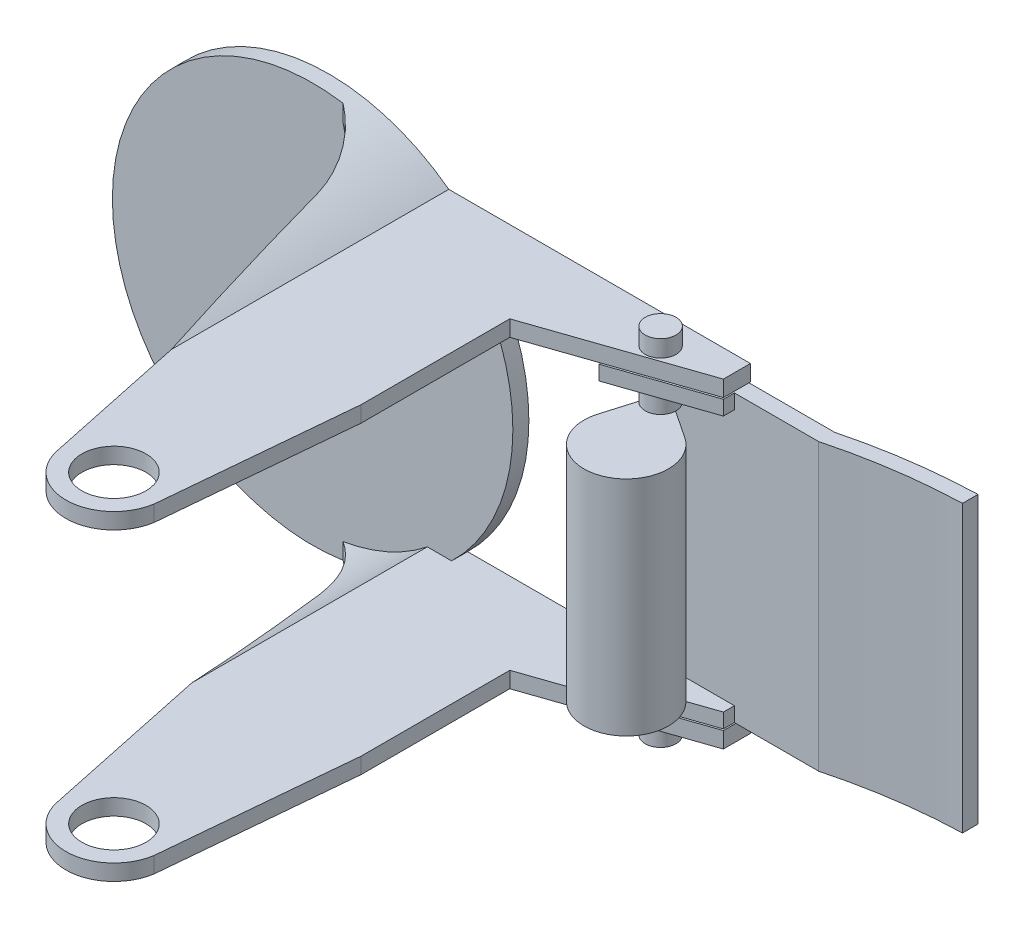
SolidWorks part; units mm, degrees
ref_plane "前视基准面" through (0, 0, 0) normal (0, 0, 1) x (1, 0, 0)
ref_plane "上视基准面" through (0, 0, 0) normal (0, 1, 0) x (1, 0, 0)
ref_plane "右视基准面" through (0, 0, 0) normal (1, 0, 0) x (0, 0, -1)
sketch "草图1" plane through (0, 0, 0) normal (0, 0, 1) x (1, 0, 0)
  line L0 (59.8768, 20) -> (63.0859, 20)
  line L1 (15, -20) -> (32.808, -20)
  line L2 (59.8768, -20) -> (59.8768, 20)
  line L3 (32.808, 20) -> (15, 20)
  line L4 (63.0859, 20) -> (63.0859, 18)
  line L5 (0, 50.776) -> (0, -82.3073)
  line L6 (63.0859, 18) -> (59.8768, 18)
  line L7 (32.808, 20) -> (32.808, 18)
  line L8 (59.8768, -20) -> (63.0859, -20)
  line L9 (63.0859, -20) -> (63.0859, -18)
  line L10 (63.0859, -18) -> (59.8768, -18)
  line L11 (32.808, 18) -> (14.3178, 18)
  line L12 (32.808, -18) -> (32.808, -20)
  line L13 (32.808, -18) -> (14.3178, -18)
  line L14 (0, 25) -> (0, 23)
  line L15 (0, -23) -> (0, -25)
  arc A1 (15, 20) -> (0, 25) centre (0, 0) ccw
  arc A2 (14.3178, 18) -> (0, 23) centre (0, 0) ccw
  arc A3 (0, -23) -> (14.3178, -18) centre (0, 0) ccw
  arc A4 (0, -25) -> (15, -20) centre (0, 0) ccw
extrude "凸台-拉伸2" add sketch "草图1" along normal blind 57.5 contours L3 A1 L14 A2 L11 L7
sketch "草图3" plane through (0, 20, 0) normal (0, 1, 0) x (1, 0, 0)
  line L0 (32.808, 0) -> (40.7234, 0)
  line L1 (40.7234, 0) -> (40.7234, -51.5)
  circle A0 centre (24.6955, -51.5) radius 4
extrude "切除-拉伸1" cut sketch "草图3" against normal blind 57.5 contours A0
sketch "草图4" plane through (0, 20, 0) normal (0, 1, 0) x (1, 0, 0)
  line L0 (32.808, -57.5) -> (15, -57.5) construction
  line L2 (30.6256, -52.4132) -> (32.808, -28.75)
  line L3 (32.808, -57.5) -> (32.808, 0) construction
  line L4 (9.6937, -10.2252) -> (18.9407, -53.1977)
  line L5 (32.808, -28.75) -> (32.808, -57.5)
  line L6 (32.808, -57.5) -> (24.6955, -57.5)
  line L7 (24.6955, -57.5) -> (0, -57.5)
  line L8 (0, -57.5) -> (0, 0)
  arc A1 (0, 0) -> (9.6937, -10.2252) centre (-2.581, -12.1543) cw
  arc A2 (24.6955, -57.5) -> (30.6256, -52.4132) centre (24.6955, -51.5) ccw
  arc A3 (18.9407, -53.1977) -> (24.6955, -57.5) centre (24.6955, -51.5) ccw
extrude "切除-拉伸3" cut sketch "草图4" against normal blind 57.5 contours A2 L2 L5 L6
sketch "草图7" plane through (0, 18, 0) normal (0, -1, 0) x (1, 0, 0)
  line L1 (18.825, 52.74) -> (10.0436, 11.1674)
  line L2 (0, 0) -> (0, 57.5)
  line L3 (0, 57.5) -> (24.6955, 57.5)
  arc A0 (24.6955, 57.5) -> (18.825, 52.74) centre (24.6955, 51.5) ccw
  arc A2 (0, 0) -> (10.0436, 11.1674) centre (-5.5103, 15.0559) ccw
  arc A3 (30.6256, 52.4132) -> (24.6955, 57.5) centre (24.6955, 51.5) ccw construction
extrude "切除-拉伸4" cut sketch "草图7" against normal blind 57.5
sketch "草图9" plane through (0, 0, 0) normal (0, 0, -1) x (-1, 0, 0)
  line L0 (0, 0) -> (-41.2693, 0)
  circle A0 centre (0, 0) radius 25
extrude "切除-拉伸5" cut sketch "草图9" against normal blind 2 contours A0
sketch "草图14" plane through (0, 0, 0) normal (0, 0, -1) x (-1, 0, 0)
  line L3 (-32.808, -18) -> (-32.808, -20)
  line L4 (-14.3178, -18) -> (-32.808, -18)
  line L5 (-15, -20) -> (-32.808, -20)
  line L7 (-3.7949, -22.6848) -> (-3.7949, -24.7103)
  arc A0 (-15, -20) -> (-3.7949, -24.7103) centre (0, 0) ccw
  arc A1 (-14.3178, -18) -> (-3.7949, -22.6848) centre (0, 0) ccw
extrude "凸台-拉伸6" add sketch "草图14" against normal blind 57.5 separate body
sketch "草图15" plane through (0, -18, 0) normal (0, 1, 0) x (1, 0, 0)
  circle A0 centre (24.6955, -51.5) radius 4
extrude "切除-拉伸6" cut sketch "草图15" against normal blind 57.5
sketch "草图16" plane through (0, -18, 0) normal (0, 1, 0) x (1, 0, 0)
  line L0 (32.808, -28.75) -> (32.808, -57.5)
  line L2 (32.808, -28.75) -> (30.6256, -52.4132)
  line L3 (32.808, -57.5) -> (24.8616, -57.5)
  line L4 (14.3178, -57.5) -> (32.808, -57.5) construction
  line L5 (24.8616, -57.4977) -> (24.8616, -57.5)
  arc A0 (18.825, -52.74) -> (30.6256, -52.4132) centre (24.6955, -51.5) ccw construction
  arc A2 (30.6256, -52.4132) -> (24.8616, -57.4977) centre (24.6955, -51.5) cw
extrude "切除-拉伸8" cut sketch "草图16" against normal blind 57.5
sketch "草图19" plane through (0, -18, 0) normal (0, 1, 0) x (1, 0, 0)
  line L0 (24.8616, -57.4977) -> (24.8616, -57.5) construction
  line L1 (24.8616, -57.4977) -> (24.8669, -57.5026)
  line L2 (24.8669, -57.5026) -> (24.8576, -57.5032)
  line L3 (24.8576, -57.5032) -> (24.4806, -57.5426)
  line L4 (24.4806, -57.5426) -> (6.9626, -59.3759)
  line L5 (6.9626, -59.3759) -> (-10.5921, -60.4492)
  line L6 (-10.5921, -60.4492) -> (-4.9283, -45.2285)
  line L7 (-4.9283, -45.2285) -> (3.7949, -2)
  line L8 (3.7949, -2) -> (10.0436, -11.1674)
  line L9 (10.0436, -11.1674) -> (18.8356, -52.7888)
  arc A0 (18.8356, -52.7888) -> (24.8616, -57.4977) centre (24.6955, -51.5) ccw
  arc A2 (18.825, -52.74) -> (30.6256, -52.4132) centre (24.6955, -51.5) ccw construction
  arc A3 (10.0436, -11.1674) -> (3.7949, -2) centre (-5.5103, -15.0559) ccw construction
extrude "切除-拉伸9" cut sketch "草图19" against normal blind 57.5
sketch "草图20" plane through (0, -18, 0) normal (0, 1, 0) x (1, 0, 0)
  line L1 (3.7949, -2) -> (3.7949, 0) construction
  line L2 (10.0436, -11.1674) -> (3.7949, -2)
  arc A0 (10.0436, -11.1674) -> (3.7949, -2) centre (-5.5103, -15.0559) ccw
extrude "切除-拉伸10" cut sketch "草图20" against normal blind 57.5
sketch "草图21" plane through (0, -18, 0) normal (0, 1, 0) x (1, 0, 0)
  line L0 (15.2952, 2.2417) -> (15, 0)
  line L1 (15, 0) -> (15, -2) construction
  line L2 (32.808, 0) -> (15, 0) construction
  line L3 (15, 0) -> (15, -2)
  line L4 (15, -2) -> (2.3979, -2)
  line L5 (2.3979, -2) -> (2.909, 1.8811)
  line L6 (2.909, 1.8811) -> (15.2952, 2.2417)
extrude "切除-拉伸11" cut sketch "草图21" against normal blind 57.5
sketch "草图23" plane through (0, 0, 0) normal (0, 0, -1) x (-1, 0, 0)
  circle A0 centre (0, 0) radius 25
extrude "凸台-拉伸7" add sketch "草图23" against normal blind 2
sketch "草图24" plane through (0, 0, 0) normal (0, 0, -1) x (-1, 0, 0)
  circle A0 centre (0, 0) radius 3.72
extrude "切除-拉伸12" cut sketch "草图24" against normal blind 2
cosmetic thread "装饰螺纹线1" parameters "D2"=10
chamfer "倒角1" distance 0.1 angle 45 2 edges at (-3.72, 0, 2) (-3.72, 0, 0)
sketch "草图26" plane through (0, -20, 0) normal (0, -1, 0) x (1, 0, 0)
  line L0 (32.808, 0) -> (52.658, 0)
  line L2 (32.808, 28.75) -> (32.808, 0) construction
  line L3 (32.808, 10.1933) -> (32.808, 0)
  line L5 (52.658, 3.3753) -> (32.808, 10.1933)
  line L8 (52.658, 0) -> (63.1835, 0)
  line L10 (78.8361, -0.297) -> (78.8361, -2.2325)
  line L11 (63.1835, 2) -> (52.658, 2)
  line L12 (52.658, 2) -> (52.658, 3.3753)
  arc A9 (63.1835, 2) -> (78.8361, -0.297) centre (81.0041, 68.9571) ccw
  arc A10 (63.1835, 0) -> (78.8361, -2.2325) centre (81.0041, 68.9571) ccw
  circle A13 centre (53.8472, 10.9778) radius 6.5409
  circle A14 centre (51.1732, 1.3095) radius 0.9616
extrude "凸台-拉伸9" add sketch "草图26" against normal blind 40 contours L10 A10 L8 L0 L3 L5 L12 L11 A13
sketch "草图28" plane through (0, -18, 0) normal (0, 1, 0) x (1, 0, 0)
  line L4 (52.658, -2) -> (52.658, 6.3503)
  line L5 (52.658, 6.3503) -> (82.0742, 6.3503)
  line L6 (82.0742, 6.3503) -> (82.0742, -4.8171)
  line L7 (82.0742, -4.8171) -> (68.0686, -9.6913)
  line L8 (68.0686, -9.6913) -> (52.658, -2)
extrude "切除-拉伸14" cut sketch "草图28" against normal blind 15
sketch "草图29" plane through (0, 18, 0) normal (0, -1, 0) x (1, 0, 0)
  line L0 (52.658, 0) -> (52.658, 7.9653)
  line L1 (52.658, 7.9653) -> (80.9235, 6.2321)
  line L2 (80.9235, 6.2321) -> (83.7158, -14.3728)
  line L3 (83.7158, -14.3728) -> (61.474, -14.3728)
  line L4 (61.474, -14.3728) -> (52.658, 0)
extrude "切除-拉伸15" cut sketch "草图29" against normal blind 15
sketch "草图30" plane through (52.658, 0, 0) normal (1, 0, 0) x (0, 0, -1)
  line L0 (-14, 16) -> (-2, 16)
  line L2 (-2, 16) -> (-2, -16)
  line L3 (-2, -16) -> (-14, -16)
  line L4 (-14, 16) -> (-14, -16)
extrude "切除-拉伸17" cut sketch "草图30" against normal blind 27
sketch "草图31" plane through (0, 0, 0) normal (0, 0, -1) x (-1, 0, 0)
  line L0 (-32.808, 18) -> (-41.1024, 18)
  line L1 (-41.1024, 18) -> (-41.1024, -18)
  line L2 (-41.1024, -18) -> (-32.808, -18)
  line L3 (-32.808, -18) -> (-32.808, 18)
extrude "切除-拉伸18" cut sketch "草图31" against normal blind 12
sketch "草图32" plane through (0, 0, 0) normal (0, 0, -1) x (-1, 0, 0)
  line L0 (-41.1024, 18) -> (-41.1024, 17.8178)
  line L1 (-41.1024, 18) -> (-41.1024, -18) construction
  line L2 (-41.1024, 17.8178) -> (-80.4808, 17.8178)
  line L3 (-80.2984, 18.1229) -> (-78.8361, 18)
  line L4 (-78.8361, 18) -> (-78.8361, -18) construction
  line L5 (-63.1835, 18) -> (-78.8361, 18) construction
  line L6 (-78.8361, 18) -> (-41.1024, 18)
  arc A0 (-80.4808, 17.8178) -> (-80.2984, 18.1229) centre (-80.1343, 17.8178) cw
extrude "切除-拉伸19" cut sketch "草图32" against normal blind 12
sketch "草图33" plane through (0, 0, 0) normal (0, 0, -1) x (-1, 0, 0)
  line L0 (-41.1024, 17.8178) -> (-41.1024, 18)
  line L1 (-52.658, 18) -> (-17.3494, 18) construction
  line L2 (-41.1024, 18) -> (-90.8654, 18)
  line L3 (-90.8654, 18) -> (-92.5652, 18)
  line L4 (-92.5652, 18) -> (-78.8361, 17.8178)
  line L5 (-78.8361, 18) -> (-78.8361, -18) construction
  line L6 (-78.8361, 17.8178) -> (-41.1024, 17.8178)
extrude "切除-拉伸20" cut sketch "草图33" along normal blind 12
sketch "草图34" plane through (0, 0, 0) normal (0, 0, -1) x (-1, 0, 0)
  line L0 (-41.1024, -18) -> (-41.1024, -17.8245)
  line L1 (-41.1024, 17.8178) -> (-41.1024, -18) construction
  line L2 (-41.1024, -17.8245) -> (-87.5995, -17.8245)
  line L3 (-87.5995, -17.8245) -> (-86.5877, -19.8267)
  line L4 (-86.5877, -19.8267) -> (-63.1835, -18)
  line L5 (-63.1835, -18) -> (-41.1024, -18)
extrude "切除-拉伸23" cut sketch "草图34" against normal blind 12
sketch "草图35" plane through (0, 0, 0) normal (0, 0, -1) x (-1, 0, 0)
  line L0 (-63.1835, -17.8245) -> (-63.0127, -20.6234)
  line L1 (-63.0127, -20.6234) -> (-79.2371, -22.4118)
  line L2 (-79.2371, -22.4118) -> (-80.6807, -17.0467)
  line L3 (-80.6807, -17.0467) -> (-78.8361, -17.8245)
  line L4 (-78.8361, 17.8178) -> (-78.8361, -18) construction
  line L5 (-78.8361, -17.8245) -> (-63.1835, -17.8245)
extrude "切除-拉伸24" cut sketch "草图35" along normal blind 20
sketch "草图36" plane through (0, 16, 0) normal (0, -1, 0) x (1, 0, 0)
  circle A0 centre (45.1163, 3.6691) radius 1.4674
extrude "切除-拉伸25" cut sketch "草图36" against normal blind 20
sketch "草图37" plane through (0, 16, 0) normal (0, -1, 0) x (1, 0, 0)
  circle A0 centre (45.1163, 3.6691) radius 1.4674
extrude "切除-拉伸26" cut sketch "草图37" along normal blind 41
sketch "草图38" plane through (0, -20, 0) normal (0, -1, 0) x (1, 0, 0)
  circle A2 centre (45.1163, 3.6691) radius 1.92
extrude "凸台-拉伸11" add sketch "草图38" along normal blind 2.1
move or copy body "实体-移动/复制1" bodies to move or copy 145 placed by mates yes parameters "D1"=0, "D2"=0, "D3"=0
sketch "草图40" plane through (0, -16, 0) normal (0, 1, 0) x (1, 0, 0)
  circle A0 centre (45.1163, -3.6691) radius 1.92
extrude "凸台-拉伸12" add sketch "草图40" along normal blind 2.1
sketch "草图41" plane through (0, 20, 0) normal (0, 1, 0) x (1, 0, 0)
  circle A0 centre (45.1163, -3.6691) radius 1.92
extrude "凸台-拉伸13" add sketch "草图41" along normal blind 2.1
sketch "草图42" plane through (0, 16, 0) normal (0, -1, 0) x (1, 0, 0)
  circle A0 centre (45.1163, 3.6691) radius 1.92
extrude "凸台-拉伸14" add sketch "草图42" along normal blind 2.1
sketch "草图44" plane through (0, 13.9, 0) normal (0, -1, 0) x (1, 0, 0)
  circle A0 centre (45.1163, 3.6691) radius 1.019
extrude "凸台-拉伸15" add sketch "草图44" along normal blind 28.1
sketch "草图45" plane through (0, -13.9, 0) normal (0, 1, 0) x (1, 0, 0)
  line L0 (45.6812, -2.8211) -> (50.4848, -6.0207)
  line L1 (44.1393, -3.3798) -> (42.5007, -8.914)
  line L2 (45.6812, -2.8211) -> (44.1393, -3.3798)
  arc A0 (42.5007, -8.914) -> (50.4848, -6.0207) centre (47.5598, -10.412) ccw
  circle A1 centre (45.1163, -3.6691) radius 1.019 construction
extrude "凸台-拉伸16" add sketch "草图45" along normal blind 2.1
sketch "草图46" plane through (0, 13.9, 0) normal (0, -1, 0) x (1, 0, 0)
  line L0 (50.4848, 6.0207) -> (45.6812, 2.8211)
  line L1 (50.4848, 6.0207) -> (45.6812, 2.8211) construction
  line L3 (42.5007, 8.914) -> (44.1959, 3.1886)
  line L4 (44.1959, 3.1886) -> (45.6812, 2.8211)
  arc A0 (50.4848, 6.0207) -> (42.5007, 8.914) centre (47.5598, 10.412) ccw
extrude "凸台-拉伸17" add sketch "草图46" along normal blind 2.1
sketch "草图48" plane through (0, -11.8, 0) normal (0, 1, 0) x (1, 0, 0)
  circle A0 centre (47.5598, -10.412) radius 5.2763
extrude "凸台-拉伸18" add sketch "草图48" along normal blind 24.1
